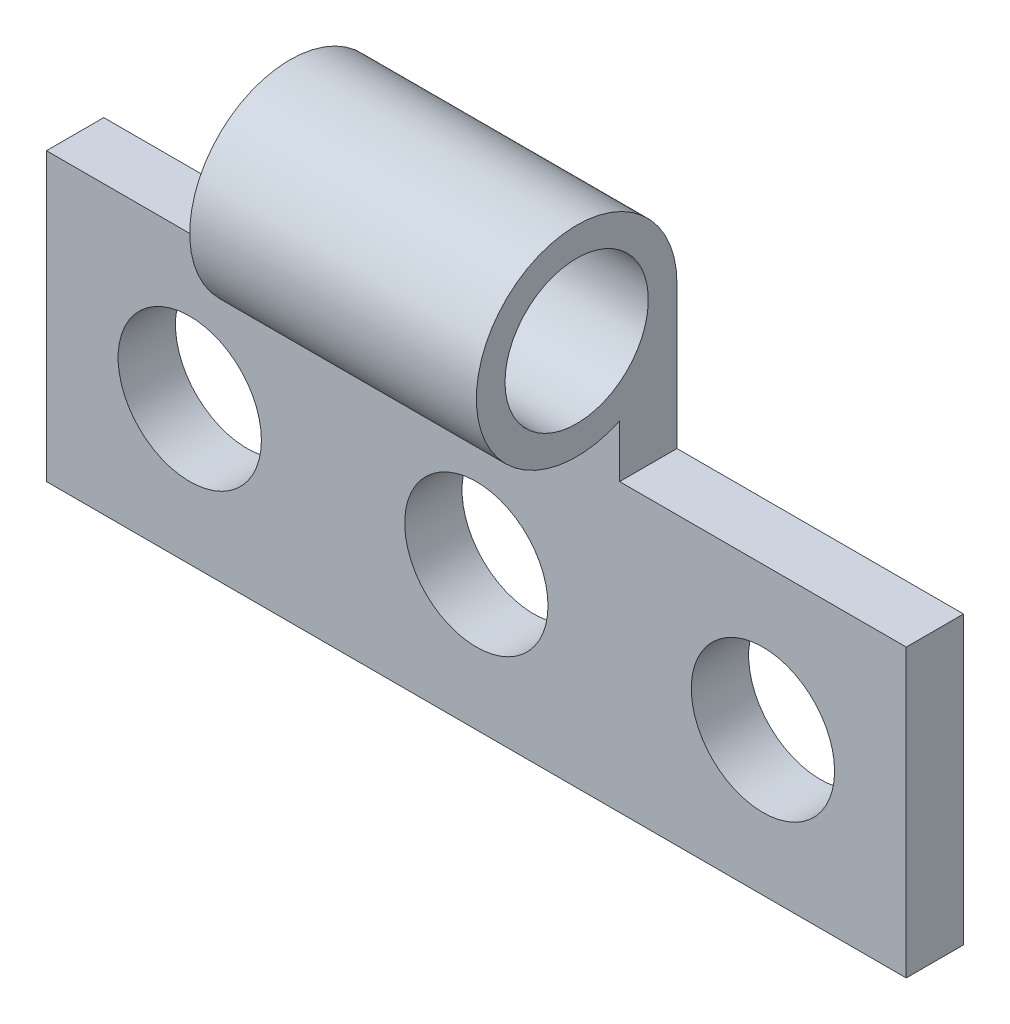
SolidWorks part; units mm, degrees
material "1060 Alloy"
ref_plane "Front Plane" through (0, 0, 0) normal (0, 0, 1) x (1, 0, 0)
ref_plane "Top Plane" through (0, 0, 0) normal (0, 1, 0) x (1, 0, 0)
ref_plane "Right Plane" through (0, 0, 0) normal (1, 0, 0) x (0, 0, -1)
sketch "Sketch1" plane through (0, 0, 0) normal (0, 0, 1) x (1, 0, 0)
  line L1 (-15, 5) -> (15, 5)
  line L2 (-15, 5) -> (-15, -5)
  line L3 (-15, -5) -> (15, -5)
  line L4 (15, 5) -> (15, -5)
  line L5 (-15, 5) -> (15, -5) construction
  line L6 (-15, -5) -> (15, 5) construction
  point P0 (0, 0)
  dimension "D1" = 30
  dimension "D2" = 10
extrude "Boss-Extrude1" add sketch "Sketch1" along normal blind 2
sketch "Sketch2" plane through (0, 0, 0) normal (-1, 0, 0) x (0, 0, 1)
  line L1 (0, 5) -> (0, 10)
  line L2 (2, 5) -> (2, 6.8377)
  line L3 (0, 5) -> (2, 5)
  arc A0 (2, 6.8377) -> (0, 10) centre (3.5, 10) ccw
  circle A1 centre (3.5, 10) radius 2.5
  dimension "D1" = 7
  dimension "D2" = 5
  dimension "D3" = 5
extrude "Boss-Extrude2" add sketch "Sketch2" against normal blind 5 and the other way blind 5
sketch "Sketch3" plane through (0, 0, 2) normal (0, 0, 1) x (1, 0, 0)
  line L0 (10, 5) -> (0, -5) construction
  line L1 (15, 5) -> (5, 5) construction
  line L2 (-15, -5) -> (15, -5) construction
  line L3 (-15, 0) -> (15, 0) construction
  line L4 (-15, 5) -> (-15, -5) construction
  line L5 (15, -5) -> (15, 5) construction
  line L6 (-10, 0) -> (0, 0) construction
  line L7 (0, 13.5) -> (0, -8.2873) construction
  line L8 (5, 13.5) -> (-5, 13.5) construction
  circle A0 centre (-10, 0) radius 2.5
  circle A1 centre (0, 0) radius 2.5
  circle A2 centre (10, 0) radius 2.5
  dimension "D1" = 5
  dimension "D2" = 5
  dimension "D4" = 10
  dimension "D3" = 3
extrude "Cut-Extrude1" cut sketch "Sketch3" against normal blind 10
